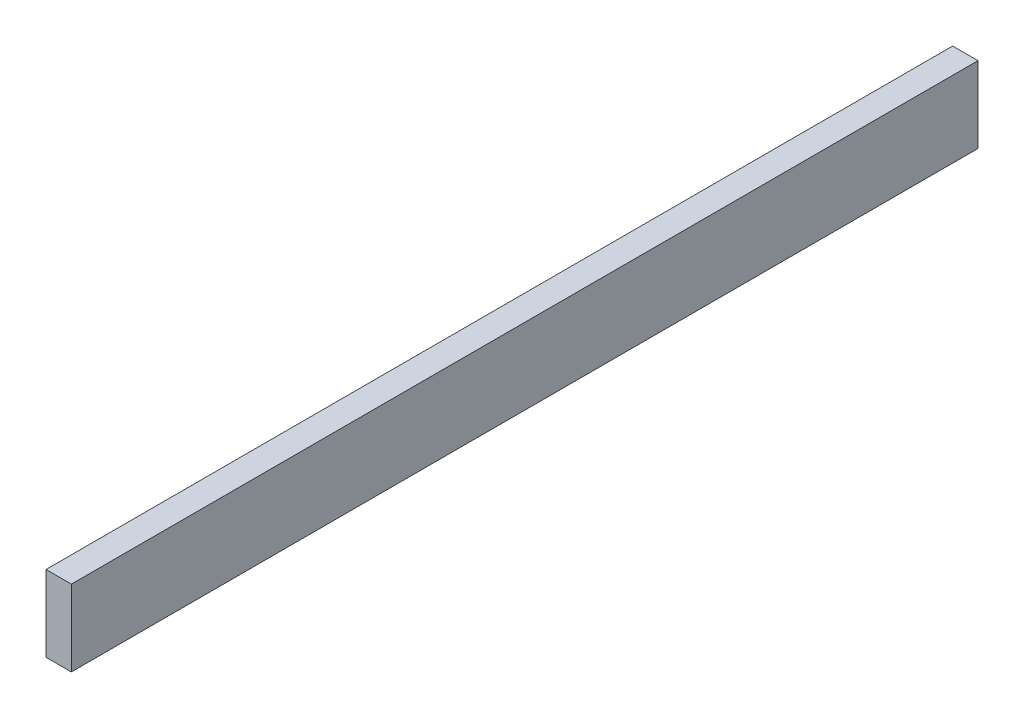
SolidWorks part; units mm, degrees
ref_plane "Front Plane" through (0, 0, 0) normal (0, 0, 1) x (1, 0, 0)
ref_plane "Top Plane" through (0, 0, 0) normal (0, 1, 0) x (1, 0, 0)
ref_plane "Right Plane" through (0, 0, 0) normal (1, 0, 0) x (0, 0, -1)
sketch "Sketch1" plane through (0, 0, 0) normal (0, 1, 0) x (1, 0, 0)
  line L1 (-10, -357.5) -> (10, -357.5)
  line L2 (-10, -357.5) -> (-10, 357.5)
  line L3 (-10, 357.5) -> (10, 357.5)
  line L4 (10, -357.5) -> (10, 357.5)
  line L5 (-10, -357.5) -> (10, 357.5) construction
  line L6 (-10, 357.5) -> (10, -357.5) construction
  point P0 (0, 0)
  dimension "D1" = 20
  dimension "D2" = 715
extrude "Boss-Extrude1" add sketch "Sketch1" along normal blind 60 contours L2 L3 L4 L1
